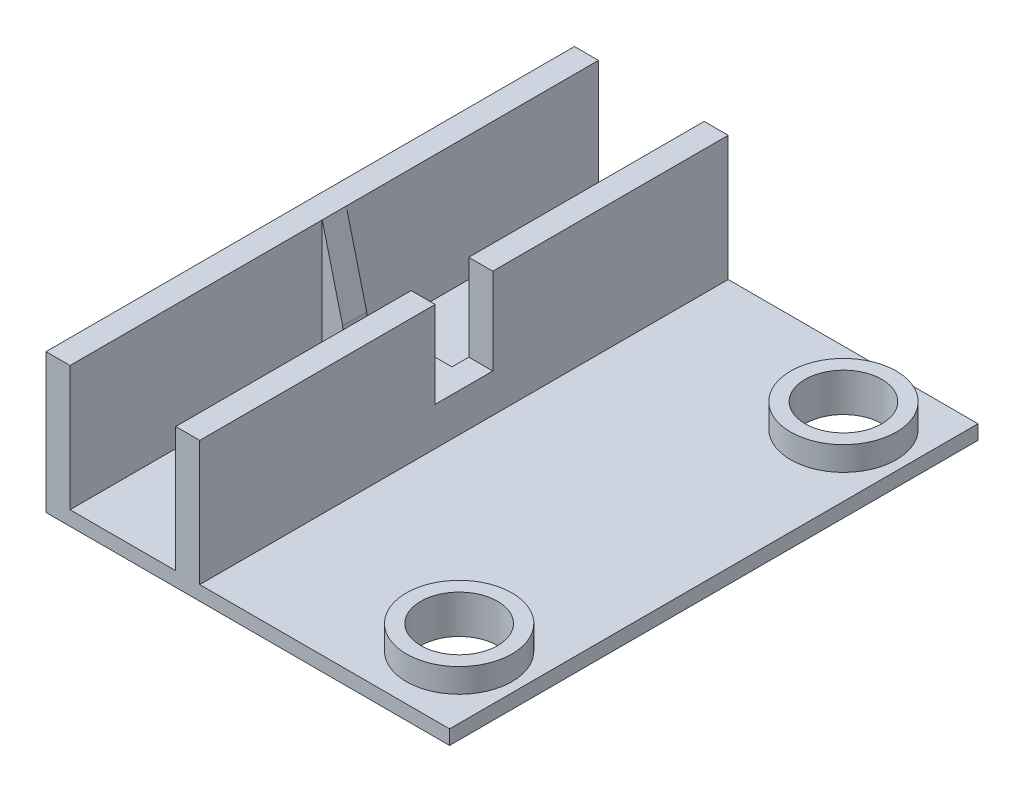
SolidWorks part; units mm, degrees
ref_plane "Front Plane" through (0, 0, 0) normal (0, 0, 1) x (1, 0, 0)
ref_plane "Top Plane" through (0, 0, 0) normal (0, 1, 0) x (1, 0, 0)
ref_plane "Right Plane" through (0, 0, 0) normal (1, 0, 0) x (0, 0, -1)
sketch "Sketch1" plane through (0, 0, 0) normal (0, 1, 0) x (1, 0, 0)
  line L1 (-21, -27.5) -> (21, -27.5)
  line L2 (-21, -27.5) -> (-21, 27.5)
  line L3 (-21, 27.5) -> (21, 27.5)
  line L4 (21, -27.5) -> (21, 27.5)
  line L5 (-21, -27.5) -> (21, 27.5) construction
  line L6 (-21, 27.5) -> (21, -27.5) construction
  point P0 (0, 0)
  dimension "D1" = 42
  dimension "D2" = 55
extrude "Boss-Extrude1" add sketch "Sketch1" along normal blind 1.5
sketch "Sketch2" plane through (0, 0, 0) normal (0, 0, 1) x (1, 0, 0)
  line L1 (-21, 1.5) -> (-5, 1.5)
  line L2 (-21, 1.5) -> (-21, 14.5)
  line L3 (-21, 14.5) -> (-5, 14.5)
  line L4 (-5, 1.5) -> (-5, 14.5)
  dimension "D1" = 16
  dimension "D2" = 13
extrude "Boss-Extrude2" add sketch "Sketch2" along normal up to surface and the other way up to surface up to face at (0, 0.75, 27.5) other way up to face at (0, 0.75, -27.5)
sketch "Sketch3" plane through (0, 0, 27.5) normal (0, 0, 1) x (1, 0, 0)
  line L0 (-21, 14.5) -> (-5, 14.5) construction
  line L1 (-18.5, 14.5) -> (-7.5, 14.5)
  line L2 (-18.5, 14.5) -> (-18.5, 1.5)
  line L3 (-18.5, 1.5) -> (-7.5, 1.5)
  line L4 (-7.5, 14.5) -> (-7.5, 1.5)
  line L5 (-21, 14.5) -> (-21, 0) construction
  line L6 (-5, 14.5) -> (-5, 1.5) construction
  dimension "D1" = 2.5
  dimension "D2" = 2.5
  dimension "D3" = 13
extrude "Cut-Extrude2" cut sketch "Sketch3" against normal through all
sketch "Sketch6" plane through (0, 0, 0) normal (0, 0, 1) x (1, 0, 0)
  line L0 (-21, 14.5) -> (-21, 0) construction
  line L1 (-5, 14.5) -> (-21, 14.5)
  line L2 (-5, 14.5) -> (-5, 1.4717)
  line L3 (-5, 1.4717) -> (-21, 1.4717)
  line L4 (-21, 14.5) -> (-21, 1.4717)
extrude "Boss-Extrude3" add sketch "Sketch6" along normal mid plane 2.5 contours L2 L3 L4 L1
sketch "Sketch7" plane through (0, 0, 1.25) normal (0, 0, 1) x (1, 0, 0)
  line L1 (-7.5, 14.5) -> (-18.5, 14.5)
  line L2 (-7.5, 14.5) -> (-9.6267, 6.0104)
  line L4 (-18.5, 14.5) -> (-16.3733, 6.0104)
  arc A0 (-16.3733, 6.0104) -> (-9.6267, 6.0104) centre (-13, 6.0104) ccw
extrude "Cut-Extrude5" cut sketch "Sketch7" against normal blind 2.5
sketch "Sketch8" plane through (-5, 0, 0) normal (1, 0, 0) x (0, 0, -1)
  line L0 (-27.5, 14.5) -> (27.5, 14.5) construction
  line L1 (-3, 14.5) -> (3, 14.5)
  line L2 (-3, 14.5) -> (-3, 5.5)
  line L3 (-3, 5.5) -> (3, 5.5)
  line L4 (3, 14.5) -> (3, 5.5)
  line L5 (0, 7.975) -> (0, -7.975) construction
  dimension "D1" = 3
  dimension "D2" = 3
  dimension "D3" = 9
extrude "Cut-Extrude6" cut sketch "Sketch8" against normal blind 6.5
sketch "Sketch9" plane through (0, 1.5, 0) normal (0, 1, 0) x (1, 0, 0)
  line L0 (-7.975, 0) -> (7.975, 0) construction
  line L1 (21, -27.5) -> (21, 27.5) construction
  circle A0 centre (14.5, 20) radius 4
  circle A1 centre (14.5, 20) radius 5.5
  dimension "D2" = 8
  dimension "D3" = 11
  dimension "D1" = 20
  dimension "D4" = 6.5
extrude "Boss-Extrude4" add sketch "Sketch9" along normal blind 2.5 contours A1 | A0
sketch "Sketch11" plane through (0, 1.5, 0) normal (0, 1, 0) x (1, 0, 0)
  circle A0 centre (14.5, 20) radius 4
extrude "Cut-Extrude7" cut sketch "Sketch11" against normal blind 2.5
mirror "Mirror1" about plane through (0, 0, 0) normal (0, 0, 1) of "Boss-Extrude4", "Cut-Extrude7"
